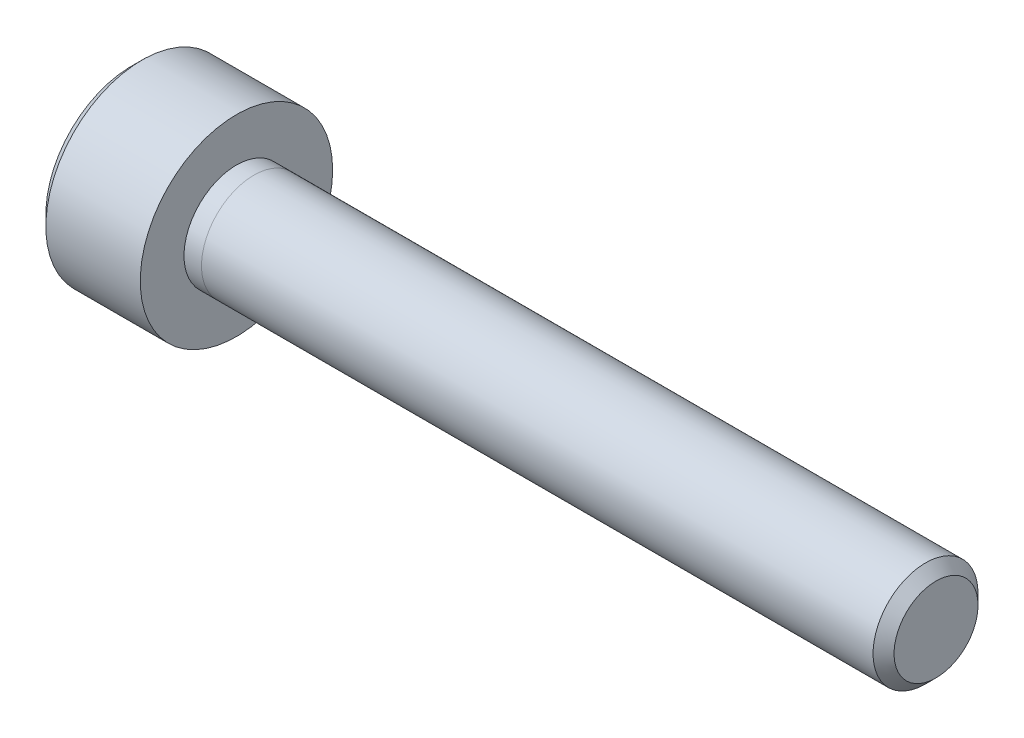
SolidWorks part; units mm, degrees
ref_plane "前视基准面" through (0, 0, 0) normal (0, 0, 1) x (1, 0, 0)
ref_plane "上视基准面" through (0, 0, 0) normal (0, 1, 0) x (1, 0, 0)
ref_plane "右视基准面" through (0, 0, 0) normal (1, 0, 0) x (0, 0, -1)
sketch "草图1" plane through (0, 0, 0) normal (1, 0, 0) x (0, 0, -1)
  circle A0 centre (0, 0) radius 2.75
  dimension "D1" = 5.5
extrude "凸台-拉伸1" add sketch "草图1" along normal blind 3
sketch "草图2" plane through (3, 0, 0) normal (1, 0, 0) x (0, 0, -1)
  circle A0 centre (0, 0) radius 1.5
  dimension "D1" = 3
extrude "凸台-拉伸2" add sketch "草图2" along normal blind 0.5
chamfer "倒角2" distance 0.3 angle 45 1 edges at (0, 0, -2.75)
sketch "草图5" plane through (0, 0, 0) normal (-1, 0, 0) x (0, 0, 1)
  line L1 (1.4307, 0.1905) -> (0.5504, 1.3343)
  line L2 (0.5504, 1.3343) -> (-0.8804, 1.1438)
  line L3 (-0.8804, 1.1438) -> (-1.4307, -0.1905)
  line L4 (-1.4307, -0.1905) -> (-0.5504, -1.3343)
  line L5 (-0.5504, -1.3343) -> (0.8804, -1.1438)
  line L6 (0.8804, -1.1438) -> (1.4307, 0.1905)
  circle A0 centre (0, 0) radius 1.25 construction
  dimension "D1" = 2.5
extrude "切除-拉伸1" cut sketch "草图5" against normal blind 2.2
sketch "草图11" plane through (3.5, 0, 0) normal (1, 0, 0) x (0, 0, -1)
  circle A0 centre (0, 0) radius 1.5
  dimension "D1" = 3
extrude "凸台-拉伸6" add sketch "草图11" along normal blind 19.5 separate body
cosmetic thread "装饰螺纹线3" parameters "D1"=8, "D2"=1.5
chamfer "倒角3" distance 0.3 angle 45 1 edges at (23, 0, -1.5)
